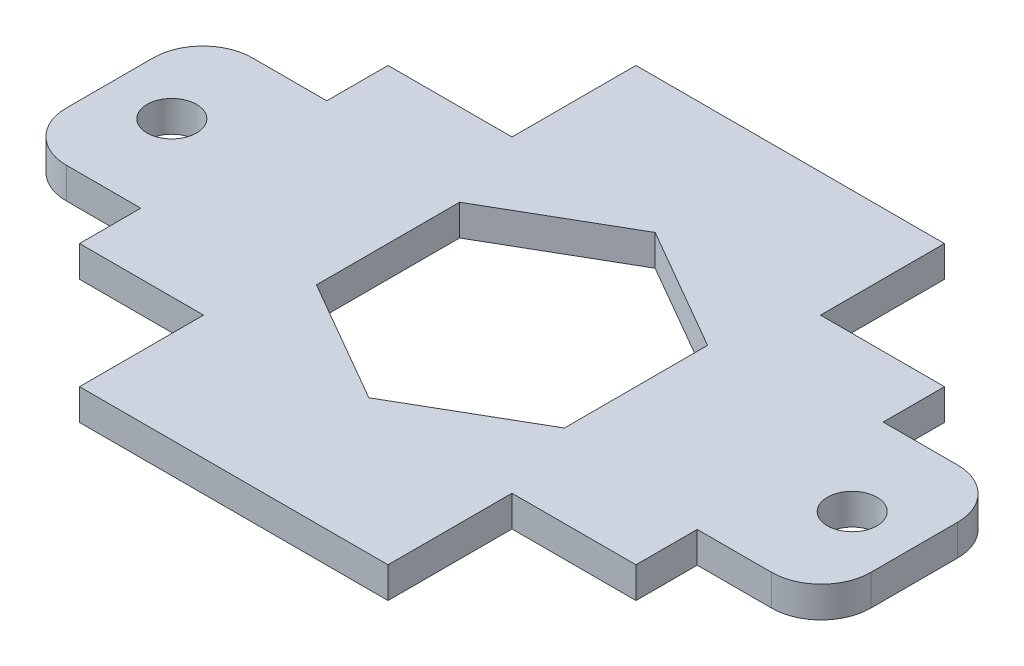
SolidWorks part; units mm, degrees
ref_plane "Front Plane" through (0, 0, 0) normal (0, 0, 1) x (1, 0, 0)
ref_plane "Top Plane" through (0, 0, 0) normal (0, 1, 0) x (1, 0, 0)
ref_plane "Right Plane" through (0, 0, 0) normal (1, 0, 0) x (0, 0, -1)
sketch "Sketch1" plane through (0, 0, 0) normal (0, 1, 0) x (1, 0, 0)
  line L5 (15.8, 15.8) -> (-15.8, -15.8) construction
  line L6 (-28.5, 15.8) -> (-28.5, 9.525)
  line L15 (-28.5, -9.525) -> (-36.12, -9.525)
  line L17 (-28.5, 9.525) -> (-36.12, 9.525)
  line L18 (-41.2, -4.445) -> (-41.2, 4.445)
  line L19 (-15.8, 28.5) -> (15.8, 28.5)
  line L20 (15.8, -28.5) -> (-15.8, -28.5)
  line L22 (15.8, -15.8) -> (-15.8, 15.8) construction
  line L23 (0, -28.5) -> (0, 28.5) construction
  line L24 (28.5, -9.525) -> (36.12, -9.525)
  line L25 (41.2, -4.445) -> (41.2, 4.445)
  line L26 (28.5, 9.525) -> (36.12, 9.525)
  line L29 (-15.8, 15.8) -> (-28.5, 15.8)
  line L30 (-15.8, 15.8) -> (-15.8, 28.5)
  line L35 (15.8, 15.8) -> (28.5, 15.8)
  line L36 (15.8, 15.8) -> (15.8, 28.5)
  line L39 (-28.5, -9.525) -> (-28.5, -15.8)
  line L40 (28.5, 15.8) -> (28.5, 9.525)
  line L41 (15.8, -15.8) -> (28.5, -15.8)
  line L42 (15.8, -15.8) -> (15.8, -28.5)
  line L45 (28.5, -9.525) -> (28.5, -15.8)
  line L47 (-15.8, -15.8) -> (-28.5, -15.8)
  line L48 (-15.8, -15.8) -> (-15.8, -28.5)
  line L53 (0, 14.6647) -> (-12.7, 7.3323)
  line L54 (-12.7, 7.3323) -> (-12.7, -7.3323)
  line L55 (-12.7, -7.3323) -> (0, -14.6647)
  line L56 (0, -14.6647) -> (12.7, -7.3323)
  line L57 (12.7, -7.3323) -> (12.7, 7.3323)
  line L58 (12.7, 7.3323) -> (0, 14.6647)
  circle A13 centre (-34.85, 0) radius 2.54
  arc A14 (36.12, -9.525) -> (41.2, -4.445) centre (36.12, -4.445) ccw
  arc A15 (41.2, 4.445) -> (36.12, 9.525) centre (36.12, 4.445) ccw
  arc A16 (-36.12, 9.525) -> (-41.2, 4.445) centre (-36.12, 4.445) ccw
  arc A17 (-36.12, -9.525) -> (-41.2, -4.445) centre (-36.12, -4.445) cw
  circle A18 centre (34.85, 0) radius 2.54
  circle A19 centre (0, 0) radius 12.7 construction
  point P0 (0, 0)
  point P9 (-28.5, 0)
  point P38 (0, 0)
  point P55 (41.2, -9.525)
  point P58 (41.2, 9.525)
  dimension "D4" = 12.7
  dimension "D5" = 25.4
  dimension "D6" = 12.7
  dimension "D10" = 6.35
  dimension "D12" = 5.08
  dimension "D13" = 5.08
  dimension "D2" = 12.7
  dimension "D3" = 82.4
  dimension "D7" = 12.7
  dimension "D9" = 19.05
  dimension "D11" = 9.525
  dimension "D8" = 12.7
  dimension "D14" = 12.7
extrude "Boss-Extrude1" add sketch "Sketch1" along normal blind 3.175
